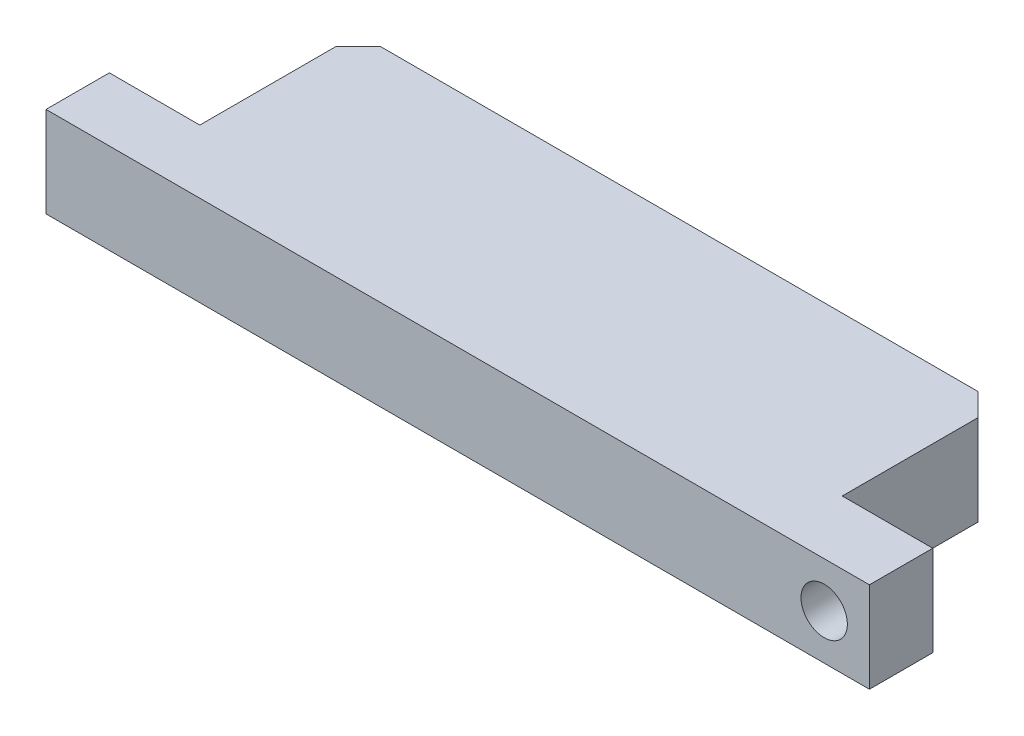
SolidWorks part; units mm, degrees
ref_plane "Front Plane" through (0, 0, 0) normal (0, 0, 1) x (1, 0, 0)
ref_plane "Top Plane" through (0, 0, 0) normal (0, 1, 0) x (1, 0, 0)
ref_plane "Right Plane" through (0, 0, 0) normal (1, 0, 0) x (0, 0, -1)
ref_plane "Plane1" through (0, 4, 0) normal (0, 1, 0) x (1, 0, 0)
sketch "Sketch1" plane through (0, 4, 0) normal (0, 1, 0) x (1, 0, 0)
  line L0 (18.2, 0) -> (-18.2, 0)
  line L1 (-18.2, 0) -> (-18.2, -9.8)
  line L2 (-18.2, -9.8) -> (18.2, -9.8)
  line L3 (18.2, -9.8) -> (18.2, 0)
extrude "Boss-Extrude1" add sketch "Sketch1" against normal blind 4
sketch "Sketch2" plane through (0, 0, 0) normal (0, -1, 0) x (1, 0, 0)
  line L0 (-14.2, 7) -> (-18.2, 7)
  line L1 (-18.2, 7) -> (-18.2, 0)
  line L2 (-18.2, 0) -> (-14.2, 0)
  line L3 (-14.2, 0) -> (-14.2, 7)
extrude "Cut-Extrude1" cut sketch "Sketch2" against normal through all
sketch "Sketch3" plane through (0, 0, 0) normal (0, -1, 0) x (1, 0, 0)
  line L0 (18.2, 7) -> (14.2, 7)
  line L1 (14.2, 7) -> (14.2, 0)
  line L2 (14.2, 0) -> (18.2, 0)
  line L3 (18.2, 0) -> (18.2, 7)
extrude "Cut-Extrude2" cut sketch "Sketch3" against normal through all
hole_wizard "Ø2.05 (2.05) Diameter Hole1" positions "Sketch5" profile "Sketch4" hole size "Ø2.05" standard "ANSI Metric"
sketch "Sketch5" plane through (0, 0, 0) normal (0, 0, -1) x (-1, 0, 0)
  point P0 (10, 2)
  point P1 (-10, 2)
sketch "Sketch4" plane through (-10, 2, 0) normal (1, 0, 0) x (0, 1, 0)
  line L0 (0, 0) -> (0, 6.9659)
  line L1 (0, 6.9659) -> (1.025, 6.35)
  line L2 (1.025, 6.35) -> (1.025, 0)
  line L5 (1.025, 0) -> (0, 0)
  line L10 (0, 6.9659) -> (-1.025, 6.35) construction
  line L11 (0, -6.35) -> (0, 107.95) construction
  dimension "Hole Dia." = 2.05
  dimension "Hole Depth" = 6.35
  dimension "Drill Angle" = 118
hole_wizard "Ø2.05 (2.05) Diameter Hole2" positions "Sketch7" profile "Sketch6" hole size "Ø2.05" standard "ANSI Metric"
sketch "Sketch7" plane through (0, 0, 9.8) normal (0, 0, 1) x (1, 0, 0)
  point P0 (16.2, 2)
sketch "Sketch6" plane through (16.2, 2, 9.8) normal (1, 0, 0) x (0, -1, 0)
  line L0 (0, 0) -> (0, 9.8)
  line L1 (0, 9.8) -> (1.025, 9.8)
  line L2 (1.025, 9.8) -> (1.025, 0)
  line L5 (1.025, 0) -> (0, 0)
  line L11 (0, -6.35) -> (0, 107.95) construction
  dimension "Thru Hole Dia." = 2.05
  dimension "Thru Hole Depth" = 9.8
chamfer "Chamfer1" distance 1 angle 45 2 edges at (-14.2, 2, 0) (14.2, 2, 0)
